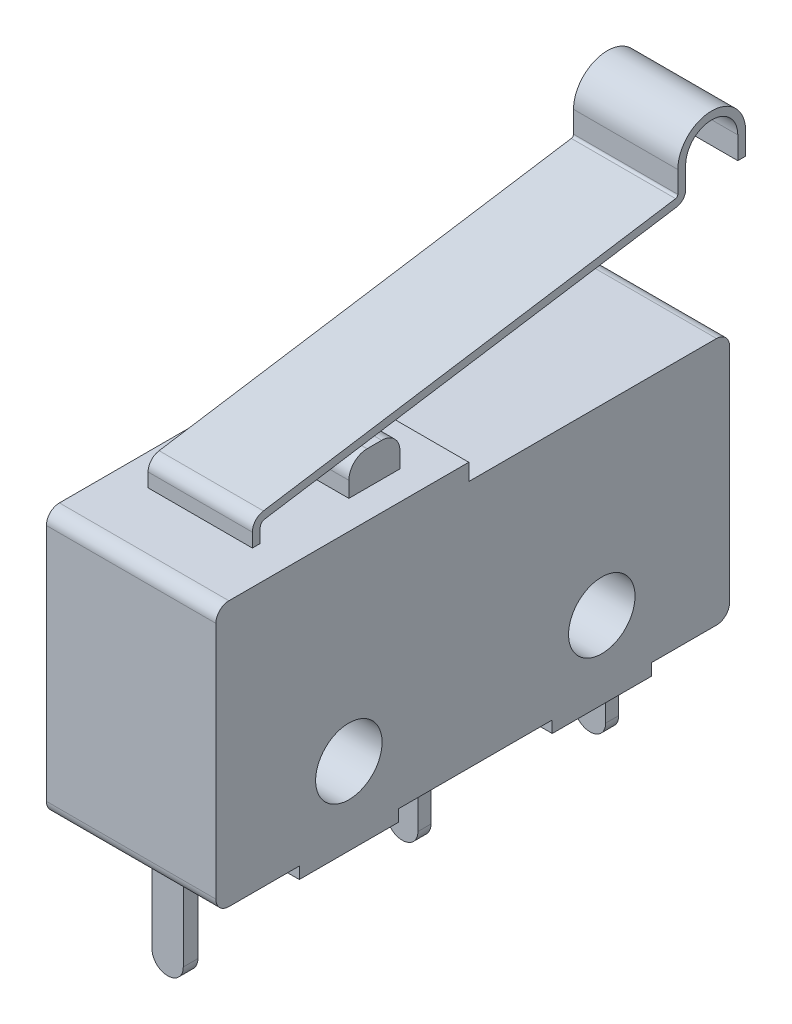
SolidWorks part; units mm, degrees
ref_plane "Front Plane" through (0, 0, 0) normal (0, 0, 1) x (1, 0, 0)
ref_plane "Top Plane" through (0, 0, 0) normal (0, 1, 0) x (1, 0, 0)
ref_plane "Right Plane" through (0, 0, 0) normal (1, 0, 0) x (0, 0, -1)
sketch "Sketch1" plane through (0, 0, 0) normal (1, 0, 0) x (0, 0, -1)
  line L0 (-9.45, 0) -> (-6.75, 0)
  line L1 (-9.95, 0.5) -> (-9.95, 9.66)
  line L2 (-9.45, 10.16) -> (-0.25, 10.16)
  line L3 (-0.25, 10.16) -> (-0.25, 9.52)
  line L4 (-0.25, 9.52) -> (9.25, 9.52)
  line L5 (9.75, 9.02) -> (9.75, 0.5)
  line L6 (-6.75, 0) -> (-6.75, -0.45)
  line L7 (-6.75, -0.45) -> (-2.95, -0.45)
  line L8 (-2.95, -0.45) -> (-2.95, 0)
  line L9 (-2.95, 0) -> (2.95, 0)
  line L10 (2.95, 0) -> (2.95, -0.45)
  line L11 (2.95, -0.45) -> (6.75, -0.45)
  line L12 (6.75, -0.45) -> (6.75, 0)
  line L13 (6.75, 0) -> (9.25, 0)
  line L14 (-4.85, -0.45) -> (-4.85, 2.525) construction
  line L15 (4.85, -0.45) -> (4.85, 2.525) construction
  line L16 (-9.95, 5.08) -> (9.75, 5.08) construction
  arc A0 (9.25, 9.52) -> (9.75, 9.02) centre (9.25, 9.02) cw
  arc A1 (9.25, 0) -> (9.75, 0.5) centre (9.25, 0.5) ccw
  arc A2 (-9.45, 0) -> (-9.95, 0.5) centre (-9.45, 0.5) cw
  arc A3 (-9.95, 9.66) -> (-9.45, 10.16) centre (-9.45, 9.66) cw
  circle A4 centre (-4.85, 2.525) radius 1.275
  circle A5 centre (4.85, 2.525) radius 1.275
  point P18 (4.85, -0.45)
  point P19 (9.75, 9.52)
  point P22 (9.75, 0)
  point P25 (-9.95, 0)
  point P28 (-9.95, 10.16)
  point P29 (-4.85, -0.45)
  point P38 (-4.85, 1.25)
  point P39 (4.85, 1.25)
  dimension "D11" = 0.5
  dimension "D12" = 2.55
  dimension "D13" = 9.52
  dimension "D2" = 10.16
  dimension "D3" = 9.7
  dimension "D4" = 3.8
  dimension "D5" = 0.45
  dimension "D6" = 0.45
  dimension "D7" = 19.7
  dimension "D8" = 3.2
  dimension "D9" = 9.7
  dimension "D10" = 5.9
  dimension "D14" = 1.7
  dimension "D15" = 1.7
extrude "Boss-Extrude1" add sketch "Sketch1" along normal blind 6.5
sketch "Sketch2" plane through (0, 10.16, 0) normal (0, 1, 0) x (1, 0, 0)
  line L0 (6.5, -0.25) -> (6.5, -9.45) construction
  line L1 (5.4, -3.75) -> (1.87, -3.75)
  line L2 (5.4, -3.75) -> (5.4, -1.79)
  line L3 (5.4, -1.79) -> (1.87, -1.79)
  line L4 (1.87, -3.75) -> (1.87, -1.79)
  line L5 (5.4, -3.75) -> (1.87, -1.79) construction
  line L6 (5.4, -1.79) -> (1.87, -3.75) construction
  line L7 (6.5, -9.95) -> (0, -9.95) construction
  point P0 (3.635, -2.77)
  dimension "D1" = 1.96
  dimension "D2" = 3.53
  dimension "D3" = 1.1
  dimension "D4" = 6.2
extrude "Boss-Extrude2" add sketch "Sketch2" along normal blind 1.3
fillet "Fillet1" radius 0.7 2 edges at (3.635, 11.46, 1.79) (3.635, 11.46, 3.75)
sketch "Sketch3" plane through (0, 0, 0) normal (0, -1, 0) x (-1, 0, 0)
  line L0 (-3.25, -9.45) -> (-3.25, 9.75) construction
  line L1 (-6.5, -9.45) -> (0, -9.45) construction
  line L2 (-6.5, 9.75) -> (0, 9.75) construction
  line L3 (-6.5, -9.95) -> (0, -9.95) construction
  line L4 (-1.65, -8.55) -> (-4.85, -8.55)
  line L5 (-1.65, -8.55) -> (-1.65, -7.99)
  line L6 (-1.65, -7.99) -> (-4.85, -7.99)
  line L7 (-4.85, -8.55) -> (-4.85, -7.99)
  line L8 (-1.65, -8.55) -> (-4.85, -7.99) construction
  line L9 (-1.65, -7.99) -> (-4.85, -8.55) construction
  line L10 (-1.65, 0.95) -> (-4.85, 0.95)
  line L11 (-1.65, 0.95) -> (-1.65, 0.45)
  line L12 (-1.65, 0.45) -> (-4.85, 0.45)
  line L13 (-4.85, 0.95) -> (-4.85, 0.45)
  line L14 (-1.65, 0.95) -> (-4.85, 0.45) construction
  line L15 (-1.65, 0.45) -> (-4.85, 0.95) construction
  line L16 (-1.65, 8.15) -> (-4.85, 8.15)
  line L17 (-1.65, 8.15) -> (-1.65, 7.65)
  line L18 (-1.65, 7.65) -> (-4.85, 7.65)
  line L19 (-4.85, 8.15) -> (-4.85, 7.65)
  line L20 (-1.65, 8.15) -> (-4.85, 7.65) construction
  line L21 (-1.65, 7.65) -> (-4.85, 8.15) construction
  point P6 (-3.25, -8.27)
  point P11 (-3.25, 0.7)
  point P16 (-3.25, 7.9)
  dimension "D1" = 3.2
  dimension "D2" = 0.56
  dimension "D3" = 3.2
  dimension "D4" = 0.5
  dimension "D5" = 3.2
  dimension "D6" = 0.5
  dimension "D7" = 1.6
  dimension "D8" = 1.4
  dimension "D9" = 6.7
extrude "Boss-Extrude3" add sketch "Sketch3" along normal blind 0.9
sketch "Sketch4" plane through (0, -0.9, 0) normal (0, -1, 0) x (-1, 0, 0)
  line L0 (-3.25, -8.55) -> (-3.25, 8.15) construction
  line L1 (-4.85, -8.55) -> (-1.65, -8.55) construction
  line L2 (-1.65, 8.15) -> (-4.85, 8.15) construction
  line L3 (-4.85, -8.55) -> (-1.65, -8.55) construction
  line L4 (-2.65, -8.55) -> (-3.85, -8.55)
  line L5 (-2.65, -8.55) -> (-2.65, -7.99)
  line L6 (-2.65, -7.99) -> (-3.85, -7.99)
  line L7 (-3.85, -8.55) -> (-3.85, -7.99)
  line L8 (-2.65, -8.55) -> (-3.85, -7.99) construction
  line L9 (-2.65, -7.99) -> (-3.85, -8.55) construction
  line L10 (-1.65, -7.99) -> (-4.85, -7.99) construction
  line L11 (-4.85, 0.45) -> (-1.65, 0.45) construction
  line L12 (-3.85, 0.95) -> (-2.65, 0.95)
  line L13 (-3.85, 0.95) -> (-3.85, 0.45)
  line L14 (-3.85, 0.45) -> (-2.65, 0.45)
  line L15 (-2.65, 0.95) -> (-2.65, 0.45)
  line L16 (-3.85, 0.95) -> (-2.65, 0.45) construction
  line L17 (-3.85, 0.45) -> (-2.65, 0.95) construction
  line L18 (-1.65, 0.95) -> (-4.85, 0.95) construction
  line L19 (-4.85, 7.65) -> (-1.65, 7.65) construction
  line L20 (-3.85, 8.15) -> (-2.65, 8.15)
  line L21 (-3.85, 8.15) -> (-3.85, 7.65)
  line L22 (-3.85, 7.65) -> (-2.65, 7.65)
  line L23 (-2.65, 8.15) -> (-2.65, 7.65)
  line L24 (-3.85, 8.15) -> (-2.65, 7.65) construction
  line L25 (-3.85, 7.65) -> (-2.65, 8.15) construction
  line L26 (-1.65, 8.15) -> (-4.85, 8.15) construction
  point P6 (-3.25, -8.27)
  point P15 (-3.25, 0.7)
  point P24 (-3.25, 7.9)
  dimension "D1" = 1.2
  dimension "D2" = 1.2
  dimension "D3" = 1.2
extrude "Boss-Extrude4" add sketch "Sketch4" along normal blind 3.47
fillet "Fillet2" radius 0.59 6 edges at (2.65, -4.37, 8.27) (3.85, -4.37, 8.27) (2.65, -4.37, -0.7) (3.85, -4.37, -0.7) (3.85, -4.37, -7.9) (2.65, -4.37, -7.9)
ref_plane "Plan1" through (3.2, 0, 0) normal (1, 0, 0) x (0, 0, -1)
sketch "Esquisse1" plane through (3.2, 0, 0) normal (1, 0, 0) x (0, 0, -1)
  line L0 (-6.7808, 10.8864) -> (9.0279, 13.3528)
  line L1 (9.0279, 13.3528) -> (11.3663, 13.7177) construction
  line L2 (-6.95, 10.6888) -> (-6.95, 10.16)
  line L3 (-0.25, 10.16) -> (-9.45, 10.16) construction
  line L5 (11.3663, 14.5737) -> (11.3663, 13.7177)
  line L6 (9.3663, 14.5737) -> (9.3663, 13.7481)
  arc A0 (-3.05, 11.46) -> (-3.75, 10.76) centre (-3.05, 10.76) ccw construction
  arc A1 (11.3663, 14.5737) -> (9.3663, 14.5737) centre (10.3663, 14.5737) ccw
  arc A2 (-6.7808, 10.8864) -> (-6.95, 10.6888) centre (-6.75, 10.6888) ccw
  arc A3 (9.0279, 13.3528) -> (9.3663, 13.7481) centre (8.9663, 13.7481) ccw
  point P13 (-6.95, 10.86)
  point P14 (10.3663, 15.5737)
  point P15 (-17.5789, 9.2017)
  point P16 (11.3663, 13.7177)
  dimension "D2" = 2
  dimension "D5" = 0.2
  dimension "D3" = 0.4
  dimension "D1" = 3
  dimension "D4" = 0.7
  dimension "D6" = 16
extrude "Extru.-Mince1" add sketch "Esquisse1" along normal blind 2 and the other way blind 2 thin
